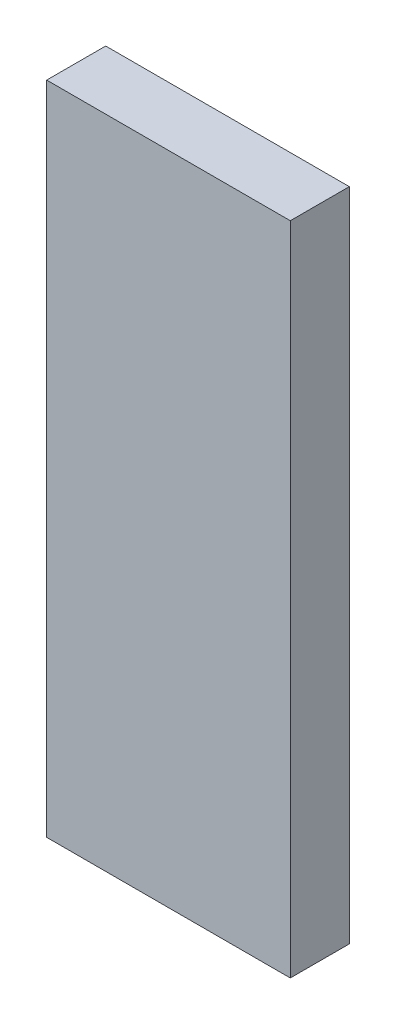
SolidWorks part; units mm, degrees
ref_plane "Front Plane" through (0, 0, 0) normal (0, 0, 1) x (1, 0, 0)
ref_plane "Top Plane" through (0, 0, 0) normal (0, 1, 0) x (1, 0, 0)
ref_plane "Right Plane" through (0, 0, 0) normal (1, 0, 0) x (0, 0, -1)
sketch "Sketch1" plane through (0, 0, 0) normal (0, 0, 1) x (1, 0, 0)
  line L1 (0, 0) -> (16.51, 0)
  line L2 (0, 0) -> (0, 44.45)
  line L3 (0, 44.45) -> (16.51, 44.45)
  line L4 (16.51, 0) -> (16.51, 44.45)
  dimension "D1" = 16.51
  dimension "D2" = 44.45
extrude "Boss-Extrude1" add sketch "Sketch1" along normal blind 4
